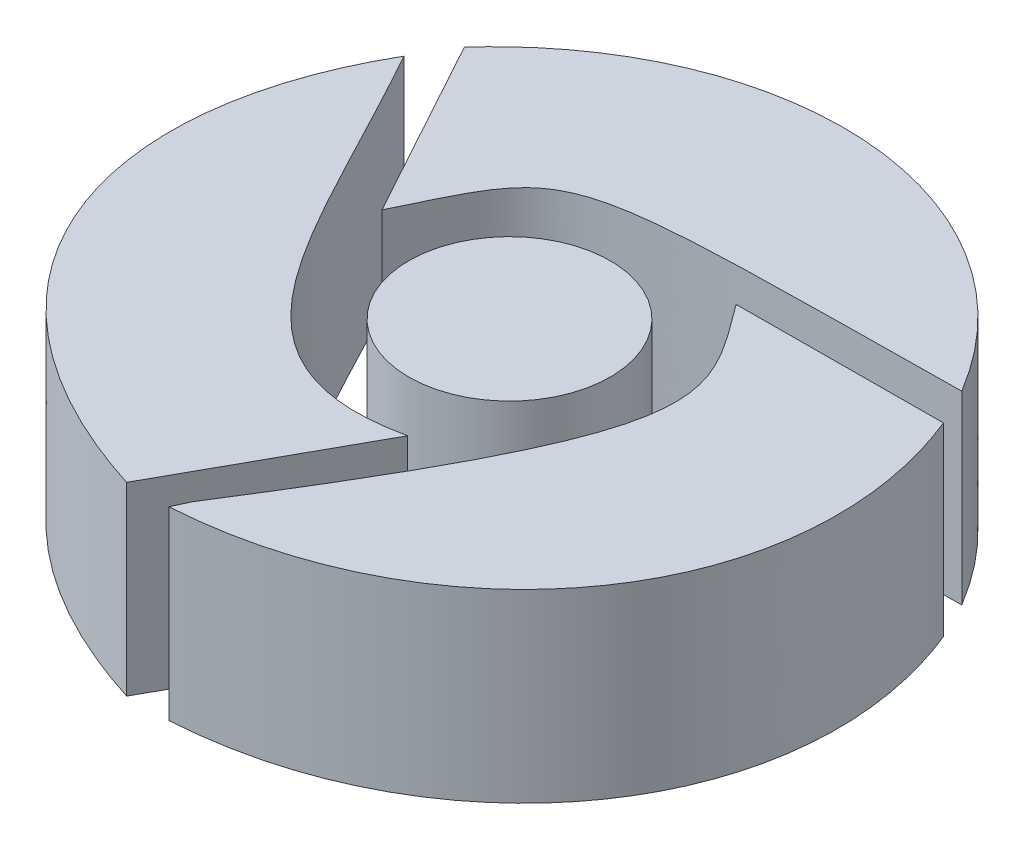
SolidWorks part; units mm, degrees
ref_plane "Front Plane" through (0, 0, 0) normal (0, 0, 1) x (1, 0, 0)
ref_plane "Top Plane" through (0, 0, 0) normal (0, 1, 0) x (1, 0, 0)
ref_plane "Right Plane" through (0, 0, 0) normal (1, 0, 0) x (0, 0, -1)
sketch "Sketch1" plane through (0, 0, 0) normal (0, 1, 0) x (1, 0, 0)
  line L0 (85.3333, 256) -> (426.6667, 256) construction
  circle A0 centre (4.4937, 4.3772) radius 1.0883
  spline S0 degree 1 poles (1.7083, 6.675) (2.7851, 4.7081) knots 0 0 1 1
  spline S1 degree 3 poles (2.7851, 4.7081) (3.503, 6.1845) (3.2506, 6.0872) (7.6122, 6.1438) knots 0 0 0 0 1 1 1 1
  spline S2 degree 3 poles (7.6122, 6.1438) (6.2549, 8.4059) (3.3905, 8.5487) (1.7083, 6.675) knots 0 0 0 0 1 1 1 1
  spline S3 degree 1 poles (5.582, 5.7366) (7.8101, 5.7479) knots 0 0 1 1
  spline S4 degree 3 poles (7.8101, 5.7479) (8.7932, 3.3159) (7.1663, 0.9519) (4.4114, 0.7803) knots 0 0 0 0 1 1 1 1
  spline S5 degree 3 poles (5.582, 5.7366) (6.3557, 4.6923) (6.6872, 4.4221) (4.4937, 0.9578) knots 0 0 0 0 1 1 1 1
  spline S6 degree 1 poles (4.4937, 0.9578) (4.4114, 0.7803) knots 0 0 1 1
  spline S7 degree 3 poles (1.4657, 6.2636) (2.6856, 4.0971) (3.1842, 2.3334) (5.0369, 2.7334) knots 0 0 0 0 1 1 1 1
  spline S8 degree 3 poles (1.4657, 6.2636) (0.26, 4.1821) (0.9733, 1.7307) (3.9549, 0.7803) knots 0 0 0 0 1 1 1 1
  spline S9 degree 1 poles (3.9549, 0.7803) (5.0369, 2.7334) knots 0 0 1 1
extrude "Boss-Extrude1" add sketch "Sketch1" along normal blind 2
